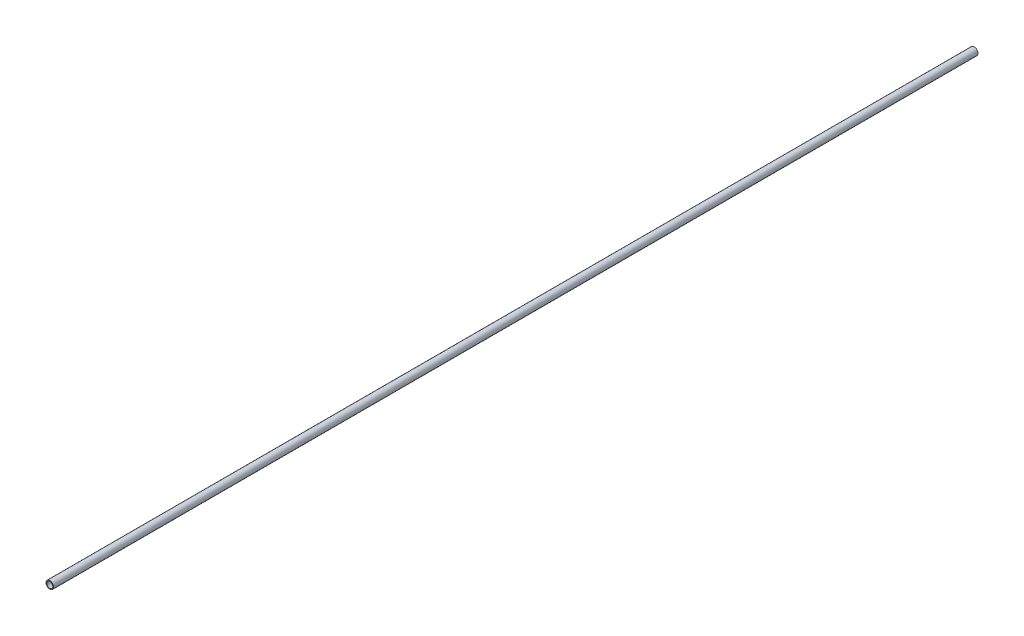
SolidWorks part; units mm, degrees
material "Thornel Mat VMA"
ref_plane "正面" through (0, 0, 0) normal (0, 0, 1) x (1, 0, 0)
ref_plane "平面" through (0, 0, 0) normal (0, 1, 0) x (1, 0, 0)
ref_plane "右側面" through (0, 0, 0) normal (1, 0, 0) x (0, 0, -1)
sketch "ｽｹｯﾁ1" plane through (0, 0, 0) normal (0, 0, 1) x (1, 0, 0)
  circle A0 centre (0, 0) radius 2
  circle A1 centre (0, 0) radius 2.5
  dimension "D1" = 5
  dimension "D2" = 0.5
extrude "ﾎﾞｽ - 押し出し1" add sketch "ｽｹｯﾁ1" along normal blind 610
